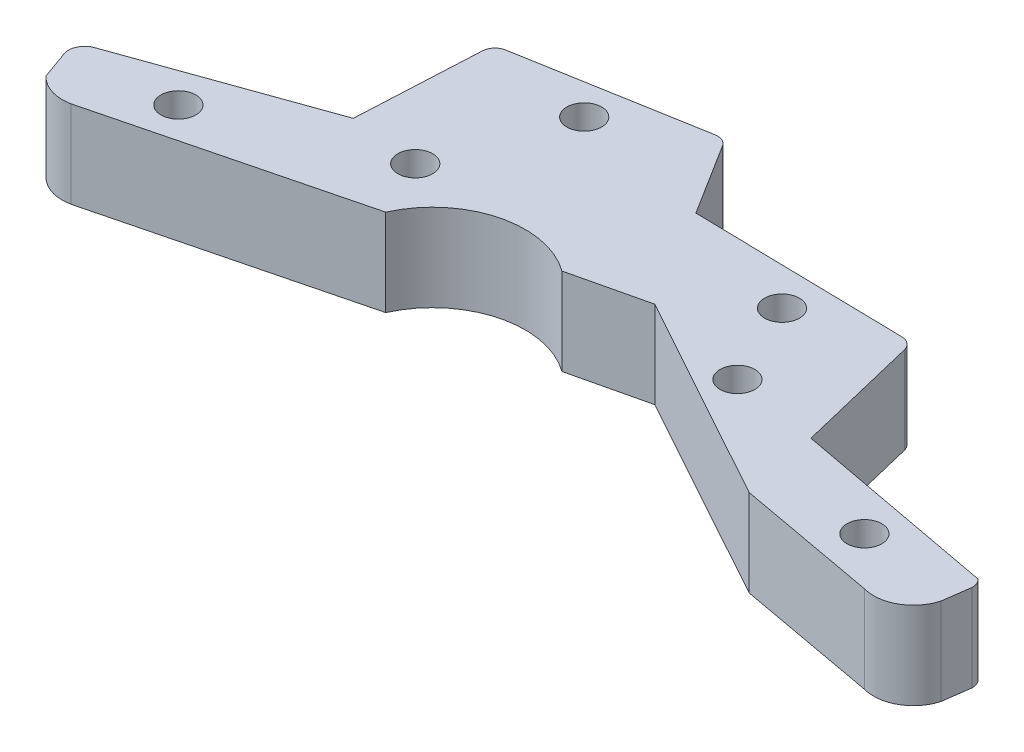
SolidWorks part; units mm, degrees
ref_plane "Front Plane" through (0, 0, 0) normal (0, 0, 1) x (1, 0, 0)
ref_plane "Top Plane" through (0, 0, 0) normal (0, 1, 0) x (1, 0, 0)
ref_plane "Right Plane" through (0, 0, 0) normal (1, 0, 0) x (0, 0, -1)
sketch "Sketch1" plane through (0, 0, 0) normal (0, 1, 0) x (1, 0, 0)
  line L0 (26.079, 92.2493) -> (666.079, 92.2493) construction
  line L17 (-1.1368, 2.0664) -> (-0.6139, 0.603)
  line L18 (28.235, 6.7336) -> (40.314, 0.0743)
  line L19 (39.3889, 4.5482) -> (51.1854, 2.3476)
  line L20 (10.3239, 7.3184) -> (10.7086, 14.9918)
  line L21 (37.4883, 12.199) -> (37.6684, 11.6588)
  line L22 (37.3426, 12.199) -> (37.4883, 12.199)
  line L23 (22.0353, 16.9807) -> (24.8826, 12.4459)
  line L24 (24.8826, 12.4459) -> (37.3426, 12.199)
  line L25 (37.8177, 11.0418) -> (37.6684, 11.6588)
  line L26 (37.8177, 11.0418) -> (39.3889, 4.5482)
  line L27 (23.9177, 5.7155) -> (28.235, 6.7336)
  line L28 (51.4411, 1.7605) -> (51.2262, 0.1865)
  line L29 (-0.7409, 3.3644) -> (10.3239, 7.3184)
  line L30 (1.4923, -0.0666) -> (15.9238, 3.5841)
  line L31 (40.314, 0.0743) -> (48.4142, -1.4039)
  line L32 (10.7086, 14.9918) -> (22.0353, 16.9807)
  circle A4 centre (34.3533, 5.3617) radius 1
  circle A12 centre (45.6778, 1.3321) radius 1
  arc A13 (15.9238, 3.5841) -> (23.9177, 5.7155) centre (20.7856, 1.4065) cw
  arc A14 (51.1854, 2.3476) -> (51.4411, 1.7605) centre (50.721, 1.7961) cw
  circle A15 centre (14.3638, 6.8404) radius 1
  circle A16 centre (32.0864, 10.1904) radius 1
  arc A17 (-0.6139, 0.603) -> (1.4923, -0.0666) centre (1.0396, 2.1566) ccw
  arc A18 (-1.1368, 2.0664) -> (-0.7409, 3.3644) centre (-0.2898, 2.5175) cw
  circle A19 centre (4.6334, 2.96) radius 1
  arc A20 (48.4142, -1.4039) -> (51.2262, 0.1865) centre (49.025, 0.7973) ccw
  circle A21 centre (16.8929, 14.0186) radius 1
  dimension "D5" = 2
  dimension "D6" = 2
  dimension "D7" = 2
  dimension "D8" = 2
  dimension "D9" = 2
  dimension "D10" = 2
  dimension "D1" = 12
  dimension "D2" = 12.46
  dimension "D3" = 11.5
  dimension "D4" = 11.75
extrude "Boss-Extrude2" add sketch "Sketch1" along normal blind 5
fillet "Fillet1" radius 0.75 3 edges at (37.4883, 2.5, -12.199) (22.0353, 2.5, -16.9807) (10.7086, 2.5, -14.9918)
